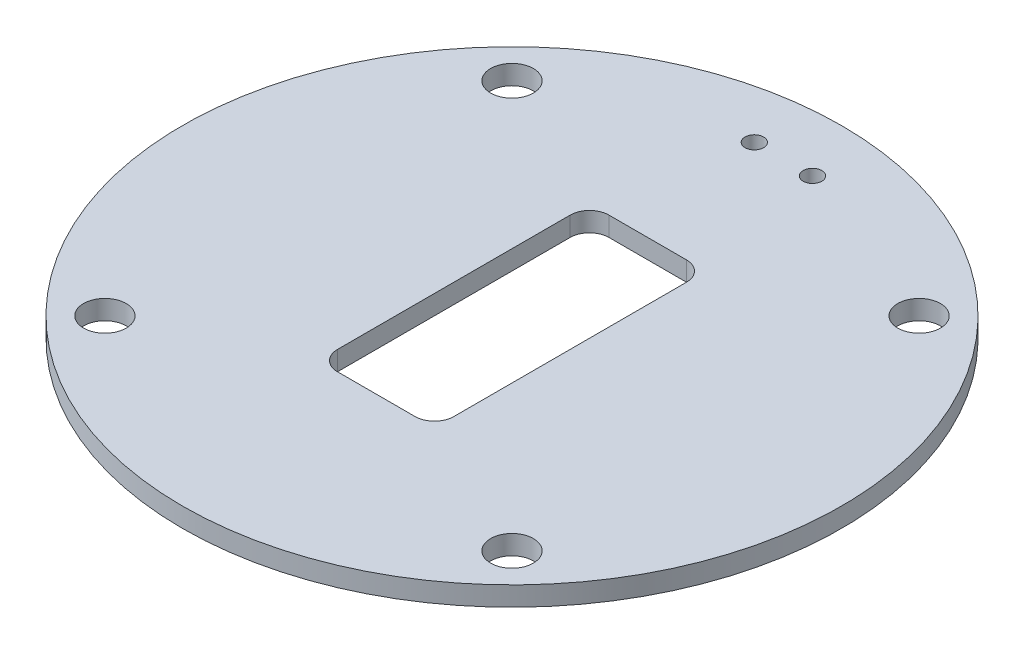
SolidWorks part; units mm, degrees
ref_plane "Front Plane" through (0, 0, 0) normal (0, 0, 1) x (1, 0, 0)
ref_plane "Top Plane" through (0, 0, 0) normal (0, 1, 0) x (1, 0, 0)
ref_plane "Right Plane" through (0, 0, 0) normal (1, 0, 0) x (0, 0, -1)
sketch "Sketch1" plane through (0, 0, 0) normal (0, 1, 0) x (1, 0, 0)
  line L0 (0, 85) -> (0, -85) construction
  line L1 (-85, 0) -> (85, 0) construction
  circle A0 centre (0, 0) radius 85
  dimension "D1" = 170
extrude "Base" add sketch "Sketch1" along normal blind 5
sketch "Sketch2" plane through (0, 5, 0) normal (0, 1, 0) x (1, 0, 0)
  line L0 (0, 85) -> (0, -85) construction
  line L1 (-85, 0) -> (85, 0) construction
  circle A6 centre (52.5, 52.5) radius 5.5
  circle A10 centre (0, 0) radius 85 construction
  circle A11 centre (-52.5, 52.5) radius 5.5
  circle A12 centre (52.5, -52.5) radius 5.5
  circle A13 centre (-52.5, -52.5) radius 5.5
  dimension "D1" = 11
  dimension "D3" = 52.5
  dimension "D2" = 52.5
extrude "Bolt Holes" cut sketch "Sketch2" against normal up to next
sketch "Sketch4" plane through (0, 5, 0) normal (0, 1, 0) x (1, 0, 0)
  line L1 (10, -35) -> (-10, -35)
  line L2 (15, -30) -> (15, 30)
  line L3 (10, 35) -> (-10, 35)
  line L4 (-15, -30) -> (-15, 30)
  line L5 (15, -35) -> (-15, 35) construction
  line L6 (15, 35) -> (-15, -35) construction
  arc A0 (15, 30) -> (10, 35) centre (10, 30) ccw
  arc A1 (10, -35) -> (15, -30) centre (10, -30) ccw
  arc A2 (-10, -35) -> (-15, -30) centre (-10, -30) cw
  arc A3 (-10, 35) -> (-15, 30) centre (-10, 30) ccw
  point P0 (0, 0)
  dimension "D1" = 5
  dimension "D2" = 30
  dimension "D3" = 70
extrude "Slot" cut sketch "Sketch4" against normal up to next
sketch "Sketch5" plane through (0, 5, 0) normal (0, 1, 0) x (1, 0, 0)
  line L0 (85, 0) -> (-85, 0) construction
  line L1 (0, 85) -> (0, -85) construction
  circle A0 centre (0, 0) radius 85 construction
  circle A1 centre (7.5, 70) radius 2.4
  circle A3 centre (-7.5, 70) radius 2.4
  dimension "D3" = 4.8
  dimension "D1" = 7.5
  dimension "D4" = 15
extrude "Switch Holes" cut sketch "Sketch5" against normal up to surface (5 mm away) up to face at (0, 0, 0)
